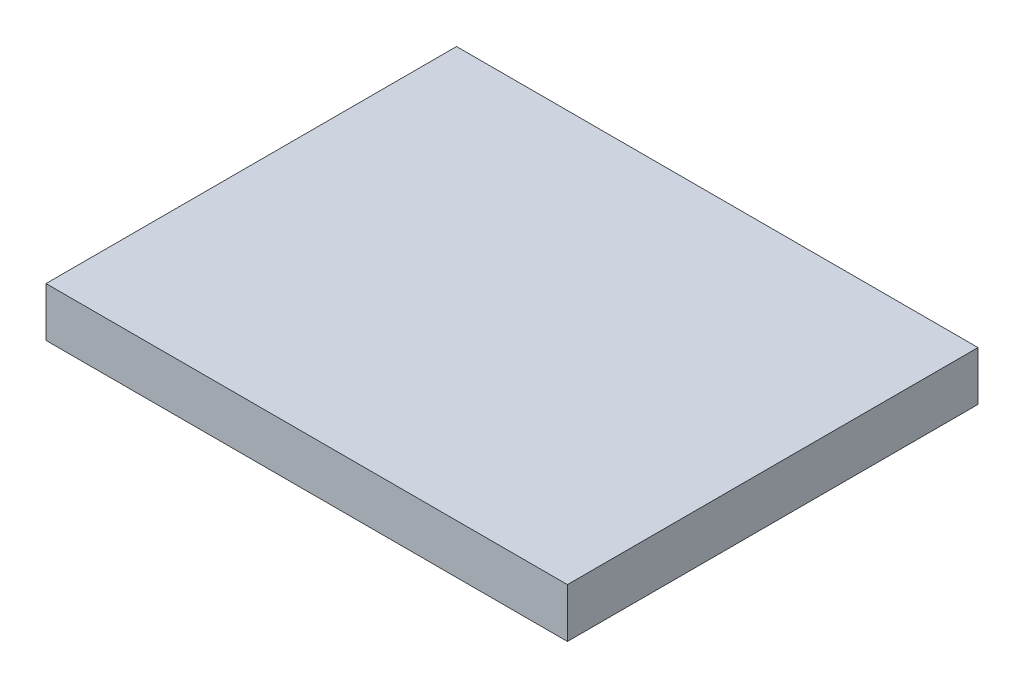
SolidWorks part; units mm, degrees
material "Melamine resin"
ref_plane "Front Plane" through (0, 0, 0) normal (0, 0, 1) x (1, 0, 0)
ref_plane "Top Plane" through (0, 0, 0) normal (0, 1, 0) x (1, 0, 0)
ref_plane "Right Plane" through (0, 0, 0) normal (1, 0, 0) x (0, 0, -1)
sketch "Sketch1" plane through (0, 0, 0) normal (0, 1, 0) x (1, 0, 0)
  line L1 (-15.875, -12.5) -> (15.875, -12.5)
  line L2 (-15.875, -12.5) -> (-15.875, 12.5)
  line L3 (-15.875, 12.5) -> (15.875, 12.5)
  line L4 (15.875, -12.5) -> (15.875, 12.5)
  line L5 (-15.875, -12.5) -> (15.875, 12.5) construction
  line L6 (-15.875, 12.5) -> (15.875, -12.5) construction
  point P0 (0, 0)
  dimension "D1" = 31.75
  dimension "D2" = 25
extrude "Boss-Extrude1" add sketch "Sketch1" along normal blind 3
